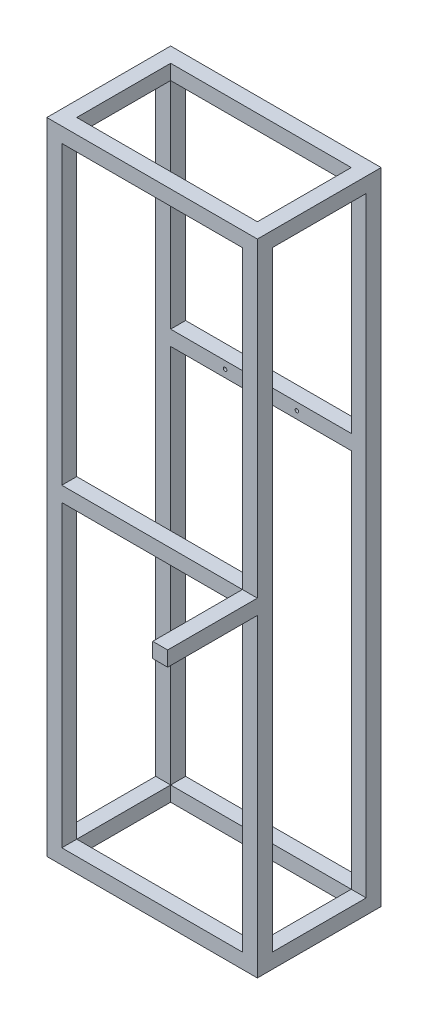
SolidWorks part; units mm, degrees
ref_plane "Спереди" through (0, 0, 0) normal (0, 0, 1) x (1, 0, 0)
ref_plane "Сверху" through (0, 0, 0) normal (0, 1, 0) x (1, 0, 0)
ref_plane "Справа" through (0, 0, 0) normal (1, 0, 0) x (0, 0, -1)
sketch "Эскиз1" plane through (0, 0, 0) normal (0, 1, 0) x (1, 0, 0)
  line L1 (0, 0) -> (352, 0)
  line L2 (0, 0) -> (0, 207)
  line L3 (0, 207) -> (352, 207)
  line L4 (352, 0) -> (352, 207)
  line L5 (25, 25) -> (327, 25)
  line L6 (25, 25) -> (25, 182)
  line L7 (25, 182) -> (327, 182)
  line L8 (327, 25) -> (327, 182)
  dimension "D1" = 352
  dimension "D2" = 207
  dimension "D3" = 25
  dimension "D4" = 25
  dimension "D5" = 25
  dimension "D6" = 25
extrude "Бобышка-Вытянуть1" add sketch "Эскиз1" along normal blind 25
sketch "Эскиз2" plane through (0, 25, 0) normal (0, 1, 0) x (1, 0, 0)
  line L1 (0, 207) -> (25, 207)
  line L2 (0, 207) -> (0, 182)
  line L3 (0, 182) -> (25, 182)
  line L4 (25, 207) -> (25, 182)
  line L5 (0, 0) -> (25, 0)
  line L6 (0, 0) -> (0, 25)
  line L7 (0, 25) -> (25, 25)
  line L8 (25, 0) -> (25, 25)
  line L9 (352, 0) -> (327, 0)
  line L10 (352, 0) -> (352, 25)
  line L11 (352, 25) -> (327, 25)
  line L12 (327, 0) -> (327, 25)
  line L13 (352, 207) -> (327, 207)
  line L14 (352, 207) -> (352, 182)
  line L15 (352, 182) -> (327, 182)
  line L16 (327, 207) -> (327, 182)
extrude "Бобышка-Вытянуть2" add sketch "Эскиз2" along normal blind 1045
sketch "Эскиз3" plane through (0, 1070, 0) normal (0, 1, 0) x (1, 0, 0)
  line L0 (0, 207) -> (352, 207)
  line L1 (352, 207) -> (352, 0)
  line L2 (352, 0) -> (0, 0)
  line L3 (0, 0) -> (0, 207)
  line L4 (25, 182) -> (25, 25)
  line L5 (25, 25) -> (327, 25)
  line L6 (327, 25) -> (327, 182)
  line L7 (327, 182) -> (25, 182)
extrude "Бобышка-Вытянуть3" add sketch "Эскиз3" against normal blind 25
sketch "Эскиз4" plane through (0, 0, -207) normal (0, 0, -1) x (-1, 0, 0)
  line L0 (-327, 1045) -> (-327, 25) construction
  line L1 (-327, 685) -> (-25, 685)
  line L2 (-327, 685) -> (-327, 660)
  line L3 (-327, 660) -> (-25, 660)
  line L4 (-25, 685) -> (-25, 660)
  line L7 (-25, 1045) -> (-25, 25) construction
  line L9 (270.3147, -65) -> (-620.6853, -65) construction
  dimension "D1" = 25
  dimension "D2" = 750
extrude "Бобышка-Вытянуть4" add sketch "Эскиз4" against normal up to vertex
sketch "Эскиз5" plane through (0, 0, 0) normal (0, 0, 1) x (1, 0, 0)
  line L0 (25, 1045) -> (25, 25) construction
  line L1 (25, 550) -> (327, 550)
  line L2 (25, 550) -> (25, 525)
  line L3 (25, 525) -> (327, 525)
  line L4 (327, 550) -> (327, 525)
  line L5 (327, 1045) -> (327, 25) construction
  line L6 (0, 0) -> (352, 0) construction
  dimension "D1" = 25
  dimension "D2" = 550
extrude "Бобышка-Вытянуть5" add sketch "Эскиз5" against normal up to vertex
sketch "Эскиз6" plane through (0, 0, 0) normal (0, 0, 1) x (1, 0, 0)
  line L0 (327, 550) -> (25, 550) construction
  line L1 (327, 550) -> (352, 550)
  line L2 (327, 550) -> (327, 525)
  line L3 (327, 525) -> (352, 525)
  line L4 (352, 550) -> (352, 525)
  line L5 (25, 525) -> (327, 525) construction
  line L6 (-270.3147, -65) -> (620.6853, -65) construction
  line L7 (-184, 1015) -> (536, 1015) construction
  line L8 (-184, 1015) -> (-184, -65) construction
  line L9 (-184, -65) -> (536, -65) construction
  line L10 (536, 1015) -> (536, -65) construction
  line L11 (176, 1015) -> (176, 1070) construction
  line L12 (0, 1070) -> (352, 1070) construction
  line L13 (352, 1070) -> (352, 0) construction
  dimension "D1" = 720
  dimension "D2" = 1080
  dimension "D3" = 25
extrude "Бобышка-Вытянуть6" add sketch "Эскиз6" along normal blind 150
sketch "Эскиз7" plane through (0, 0, -207) normal (0, 0, -1) x (-1, 0, 0)
  line L0 (-327, 685) -> (-327, 660) construction
  line L1 (-176, 685) -> (-176, 660) construction
  line L2 (-25, 685) -> (-25, 660) construction
  line L3 (-25, 685) -> (-327, 685) construction
  line L4 (-327, 672.5) -> (-25, 672.5) construction
  line L5 (-327, 660) -> (-25, 660) construction
  circle A0 centre (-236, 672.5) radius 3
  circle A1 centre (-116, 672.5) radius 3
  dimension "D1" = 120
  dimension "D3" = 6
  dimension "D2" = 60
extrude "Вырез-Вытянуть1" cut sketch "Эскиз7" against normal up to next
